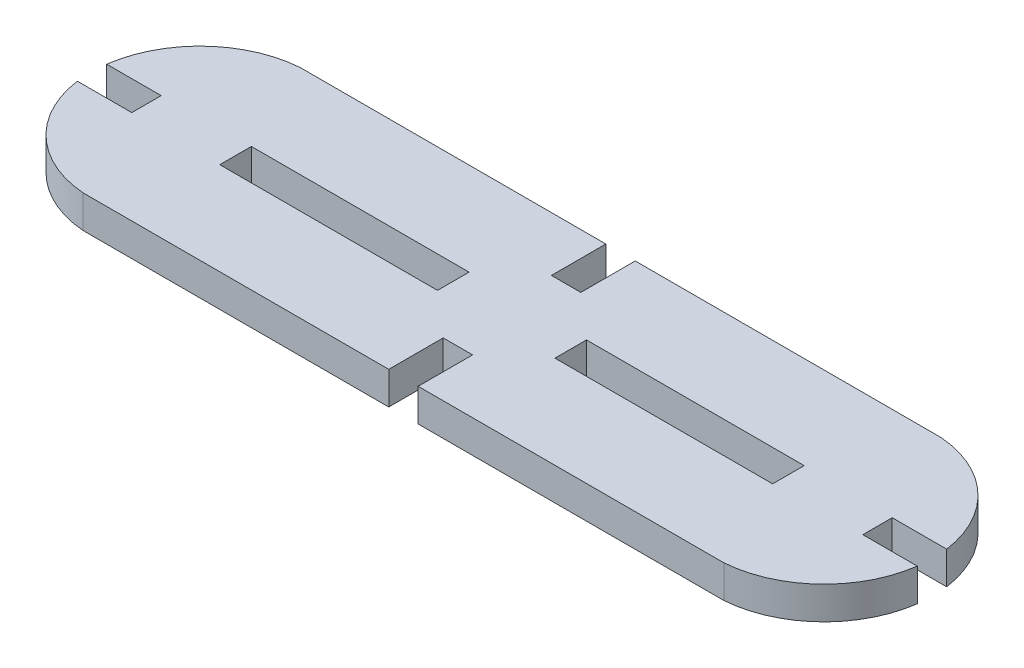
SolidWorks part; units mm, degrees
ref_plane "Alzado" through (0, 0, 0) normal (0, 0, 1) x (1, 0, 0)
ref_plane "Planta" through (0, 0, 0) normal (0, 1, 0) x (1, 0, 0)
ref_plane "Vista lateral" through (0, 0, 0) normal (1, 0, 0) x (0, 0, -1)
sketch "Sketch1" plane through (0, 0, 0) normal (0, 1, 0) x (1, 0, 0)
  line L0 (48.4783, 121.7343) -> (242.3913, 121.7343) construction
  line L1 (-50, 30) -> (-21.914, 30)
  line L10 (-54.1419, 18.6794) -> (-54.1419, 21.3794)
  line L11 (-54.1419, 21.3794) -> (-59.1419, 21.3794)
  line L12 (-21.914, 30) -> (-21.914, 25)
  line L13 (8.872, 30) -> (-19.214, 30)
  line L14 (-21.914, 25) -> (-19.214, 25)
  line L15 (-19.214, 25) -> (-19.214, 30)
  line L20 (13.0139, 18.6794) -> (13.0139, 21.3794)
  line L21 (13.0139, 21.3794) -> (18.0139, 21.3794)
  line L22 (-78.577, 20.0294) -> (30.4776, 20.0294) construction
  line L23 (13.0139, 18.6794) -> (18.0139, 18.6794)
  line L28 (-19.214, 15.0589) -> (-19.214, 10.0589)
  line L29 (-21.914, 15.0589) -> (-19.214, 15.0589)
  line L30 (8.872, 10.0589) -> (-19.214, 10.0589)
  line L31 (-21.914, 10.0589) -> (-21.914, 15.0589)
  line L32 (-54.1419, 18.6794) -> (-59.1419, 18.6794)
  line L33 (-50, 10.0589) -> (-21.914, 10.0589)
  arc A2 (-50, 30) -> (-59.1419, 21.3794) centre (-49.2334, 20.0294) ccw
  arc A3 (8.872, 30) -> (18.0139, 21.3794) centre (8.1054, 20.0294) cw
  arc A4 (8.872, 10.0589) -> (18.0139, 18.6794) centre (8.1054, 20.0294) ccw
  arc A5 (-50, 10.0589) -> (-59.1419, 18.6794) centre (-49.2334, 20.0294) cw
  point P2 (0, 0)
  point P13 (-5.171, 30)
  point P20 (-5.171, 10.0589)
  point P30 (13.0139, 20.0294)
  point P39 (-54.1419, 20.0294)
extrude "Boss-Extrude1" add sketch "Sketch1" along normal blind 3
sketch "Sketch2" plane through (0, 3, 0) normal (0, 1, 0) x (1, 0, 0)
  line L0 (-65.4402, 20.0294) -> (23.5089, 20.0294) construction
  line L1 (-35.957, 30) -> (-35.957, 10.0589) construction
  line L2 (-5.171, 30) -> (-5.171, 10.0589) construction
  line L4 (-45.957, 18.5794) -> (-25.957, 18.5794)
  line L5 (-45.957, 18.5794) -> (-45.957, 21.4794)
  line L6 (-45.957, 21.4794) -> (-25.957, 21.4794)
  line L7 (-25.957, 18.5794) -> (-25.957, 21.4794)
  line L8 (-45.957, 18.5794) -> (-25.957, 21.4794) construction
  line L9 (-45.957, 21.4794) -> (-25.957, 18.5794) construction
  line L10 (-15.171, 18.5794) -> (4.829, 18.5794)
  line L11 (-15.171, 18.5794) -> (-15.171, 21.4794)
  line L12 (-15.171, 21.4794) -> (4.829, 21.4794)
  line L13 (4.829, 18.5794) -> (4.829, 21.4794)
  line L14 (-15.171, 18.5794) -> (4.829, 21.4794) construction
  line L15 (-15.171, 21.4794) -> (4.829, 18.5794) construction
  line L16 (8.872, 30) -> (-19.214, 30)
  line L17 (-19.214, 30) -> (-19.214, 25)
  line L18 (-19.214, 25) -> (-21.914, 25)
  line L19 (-21.914, 25) -> (-21.914, 30)
  line L20 (-21.914, 30) -> (-50, 30)
  line L21 (-59.1419, 21.3794) -> (-54.1419, 21.3794)
  line L22 (-54.1419, 21.3794) -> (-54.1419, 18.6794)
  line L23 (-54.1419, 18.6794) -> (-59.1419, 18.6794)
  line L24 (-50, 10.0589) -> (-21.914, 10.0589)
  line L25 (-21.914, 10.0589) -> (-21.914, 15.0589)
  line L26 (-21.914, 15.0589) -> (-19.214, 15.0589)
  line L27 (-19.214, 15.0589) -> (-19.214, 10.0589)
  line L28 (-19.214, 10.0589) -> (8.872, 10.0589)
  line L29 (18.0139, 18.6794) -> (13.0139, 18.6794)
  line L30 (13.0139, 18.6794) -> (13.0139, 21.3794)
  line L31 (13.0139, 21.3794) -> (18.0139, 21.3794)
  line L32 (8.872, 30) -> (-19.214, 30) construction
  line L33 (-19.214, 30) -> (-19.214, 25) construction
  line L34 (-19.214, 25) -> (-21.914, 25) construction
  line L35 (-21.914, 25) -> (-21.914, 30) construction
  line L36 (-21.914, 30) -> (-50, 30) construction
  line L37 (-59.1419, 21.3794) -> (-54.1419, 21.3794) construction
  line L38 (-54.1419, 21.3794) -> (-54.1419, 18.6794) construction
  line L39 (-54.1419, 18.6794) -> (-59.1419, 18.6794) construction
  line L40 (-50, 10.0589) -> (-21.914, 10.0589) construction
  line L41 (-21.914, 10.0589) -> (-21.914, 15.0589) construction
  line L42 (-21.914, 15.0589) -> (-19.214, 15.0589) construction
  line L43 (-19.214, 15.0589) -> (-19.214, 10.0589) construction
  line L44 (-19.214, 10.0589) -> (8.872, 10.0589) construction
  line L45 (18.0139, 18.6794) -> (13.0139, 18.6794) construction
  line L46 (13.0139, 18.6794) -> (13.0139, 21.3794) construction
  line L47 (13.0139, 21.3794) -> (18.0139, 21.3794) construction
  arc A4 (18.0139, 21.3794) -> (8.872, 30) centre (8.1054, 20.0294) ccw
  arc A5 (-50, 30) -> (-59.1419, 21.3794) centre (-49.2334, 20.0294) ccw
  arc A6 (-59.1419, 18.6794) -> (-50, 10.0589) centre (-49.2334, 20.0294) ccw
  arc A7 (8.872, 10.0589) -> (18.0139, 18.6794) centre (8.1054, 20.0294) ccw
  arc A8 (18.0139, 21.3794) -> (8.872, 30) centre (8.1054, 20.0294) ccw construction
  arc A9 (-50, 30) -> (-59.1419, 21.3794) centre (-49.2334, 20.0294) ccw construction
  arc A10 (-59.1419, 18.6794) -> (-50, 10.0589) centre (-49.2334, 20.0294) ccw construction
  arc A11 (8.872, 10.0589) -> (18.0139, 18.6794) centre (8.1054, 20.0294) ccw construction
  point P20 (-35.957, 20.0294)
  point P29 (-5.171, 20.0294)
extrude "Cut-Extrude1" cut sketch "Sketch2" against normal up to next
equation "\"material\"= 3"
equation "\"kerf\"= \"material\" - 0.3mm"
equation "\"D2@Sketch1\"=\"kerf\""
equation "\"D4@Sketch1\"=\"kerf\"/2"
equation "\"D6@Sketch1\"=\"kerf\"/2"
equation "\"large\"= 90"
equation "\"Radius\"= 10"
equation "\"D4@Sketch2\"=\"subkerf\""
equation "\"D5@Sketch2\"=\"subkerf\""
equation "\"D1@Boss-Extrude1\"=\"material\""
equation "\"subkerf\"= \"material\" - 0.1mm"
